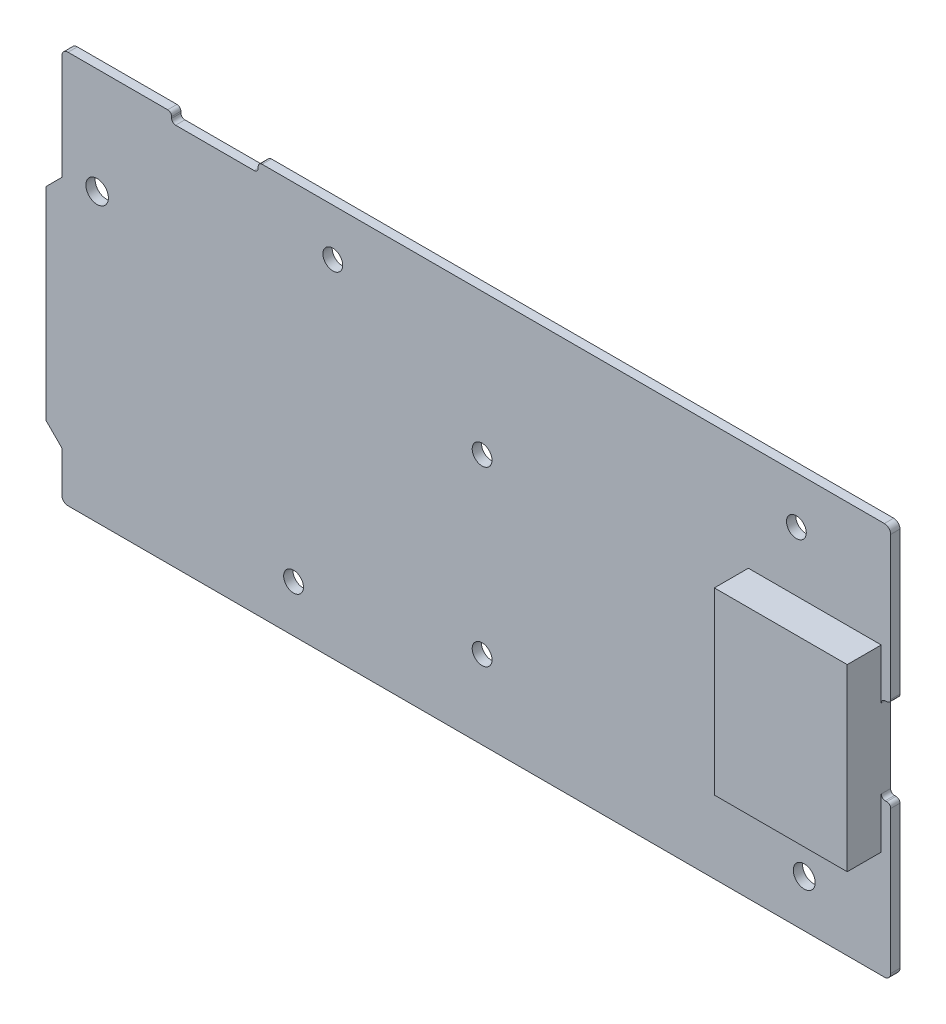
SolidWorks part; units mm, degrees
ref_plane "Plano frontal" through (0, 0, 0) normal (0, 0, 1) x (1, 0, 0)
ref_plane "Plano superior" through (0, 0, 0) normal (0, 1, 0) x (1, 0, 0)
ref_plane "Plano direito" through (0, 0, 0) normal (1, 0, 0) x (0, 0, -1)
sketch "Esboço2" plane through (0, 0, 0) normal (0, 0, 1) x (1, 0, 0)
  line L0 (66.7708, -1.788) -> (66.5169, -1.788)
  line L1 (65.8819, -1.153) -> (65.8819, 11.567)
  line L2 (66.5169, 12.202) -> (66.7709, 12.202)
  line L3 (67.4059, 12.837) -> (67.4059, 35.941)
  line L4 (66.3884, 36.957) -> (-34.1931, 36.957)
  line L5 (-34.8281, 36.3219) -> (-34.8281, 36.068)
  line L6 (-35.4632, 35.433) -> (-48.1831, 35.433)
  line L7 (-48.8181, 36.068) -> (-48.8181, 36.322)
  line L8 (-49.4532, 36.957) -> (-65.5631, 36.957)
  line L9 (-66.5791, 35.9396) -> (-66.5791, 18.923)
  line L10 (-66.5791, 18.923) -> (-69.1191, 16.383)
  line L11 (-69.1191, 16.383) -> (-69.1191, -16.383)
  line L12 (-69.1191, -16.383) -> (-66.5791, -18.923)
  line L13 (-66.5791, -18.923) -> (-66.5791, -25.527)
  line L14 (-65.5617, -26.543) -> (66.3899, -26.543)
  line L15 (67.4059, -25.5256) -> (67.4059, -2.423)
  circle A0 centre (-60.8641, 19.812) radius 1.8201
  circle A1 centre (-22.7641, 29.337) radius 1.6002
  circle A2 centre (1.3659, 14.097) radius 1.6002
  circle A3 centre (-29.1141, -18.923) radius 1.6002
  circle A4 centre (1.3659, -13.843) radius 1.6002
  circle A5 centre (52.1659, 29.337) radius 1.6002
  circle A6 centre (53.4359, -18.923) radius 1.7683
  arc A7 (67.4059, -2.423) -> (66.7708, -1.788) centre (66.7708, -2.423) ccw
  arc A8 (65.8819, -1.153) -> (66.5169, -1.788) centre (66.5169, -1.153) ccw
  arc A9 (66.5169, 12.202) -> (65.8819, 11.567) centre (66.5169, 11.567) ccw
  arc A10 (66.7709, 12.202) -> (67.4059, 12.837) centre (66.7708, 12.837) ccw
  arc A11 (67.4059, 35.941) -> (66.3884, 36.957) centre (66.3884, 35.9396) ccw
  arc A12 (-34.1931, 36.957) -> (-34.8281, 36.3219) centre (-34.1931, 36.3219) ccw
  arc A13 (-35.4632, 35.433) -> (-34.8281, 36.068) centre (-35.4632, 36.068) ccw
  arc A14 (-48.8181, 36.068) -> (-48.1831, 35.433) centre (-48.1831, 36.068) ccw
  arc A15 (-48.8181, 36.322) -> (-49.4532, 36.957) centre (-49.4532, 36.3219) ccw
  arc A16 (-65.5631, 36.957) -> (-66.5791, 35.9396) centre (-65.5617, 35.9396) ccw
  arc A17 (-66.5791, -25.527) -> (-65.5617, -26.543) centre (-65.5617, -25.5256) ccw
  arc A18 (66.3899, -26.543) -> (67.4059, -25.5256) centre (66.3884, -25.5256) ccw
extrude "Ressalto-extrusão1" add sketch "Esboço2" along normal blind 1.5
sketch "Arquivos locais1" plane through (0, 0, 0) normal (0, 0, -1) x (-1, 0, 0)
  line L2 (43.0791, -18.923) -> (43.0791, -25.527)
  line L3 (43.0791, -18.923) -> (43.0791, -25.527) construction
  line L4 (53.5791, -18.923) -> (53.5791, -25.527) construction
  line L5 (65.5617, -22.043) -> (-66.3899, -22.043)
  line L6 (65.5617, -22.043) -> (-66.3899, -22.043) construction
  line L7 (65.5617, -13.043) -> (-66.3899, -13.043) construction
  circle A0 centre (43.0791, -13.043) radius 1.5
  circle A1 centre (53.5791, -13.043) radius 1.5
  circle A2 centre (43.0791, -22.043) radius 1.5
  circle A5 centre (53.5791, -22.043) radius 1.5
  dimension "D5" = 3
  dimension "D1" = 23.5
  dimension "D2" = 4.5
  dimension "D3" = 10.5
  dimension "D4" = 9
extrude "Ressalto-extrusão2" add sketch "Arquivos locais1" along normal blind 2.5
sketch "Arquivos locais2" plane through (0, 0, 0) normal (0, 0, -1) x (-1, 0, 0)
  line L1 (66.5791, 36.957) -> (54.5791, 36.957) construction
  line L2 (66.5791, 36.957) -> (66.5791, 24.957) construction
  line L3 (66.5791, 24.957) -> (54.5791, 24.957) construction
  line L4 (54.5791, 36.957) -> (54.5791, 24.957) construction
  line L5 (54.5791, 24.957) -> (66.5791, 24.957)
  line L6 (54.5791, 24.957) -> (54.5791, 31.8918)
  line L7 (54.5791, 31.8918) -> (66.5791, 31.8918)
  line L8 (66.5791, 24.957) -> (66.5791, 31.8918)
  dimension "D1" = 12
  dimension "D2" = 12
extrude "Ressalto-extrusão3" add sketch "Arquivos locais2" along normal blind 0.2
sketch "Arquivos locais3" plane through (0, 0, 1.5) normal (0, 0, 1) x (1, 0, 0)
  line L1 (65.8819, 5.207) -> (36.0198, 5.207) construction
  line L2 (44.4059, 12.837) -> (44.4059, 35.941)
  line L3 (44.4059, 12.837) -> (44.4059, 35.941) construction
  line L4 (65.8819, -1.153) -> (65.8819, 11.567) construction
  line L5 (65.8819, 19.707) -> (36.0198, 19.707) construction
  line L6 (65.8819, -9.293) -> (36.0198, -9.293) construction
  line L8 (44.4059, 19.707) -> (65.8819, 19.707)
  line L9 (44.4059, 19.707) -> (44.4059, -9.293)
  line L10 (44.4059, -9.293) -> (65.8819, -9.293)
  line L11 (65.8819, 19.707) -> (65.8819, -9.293)
  dimension "D1" = 23
  dimension "D2" = 14.5
  dimension "D3" = 14.5
extrude "Ressalto-extrusão4" add sketch "Arquivos locais3" along normal blind 5.5
